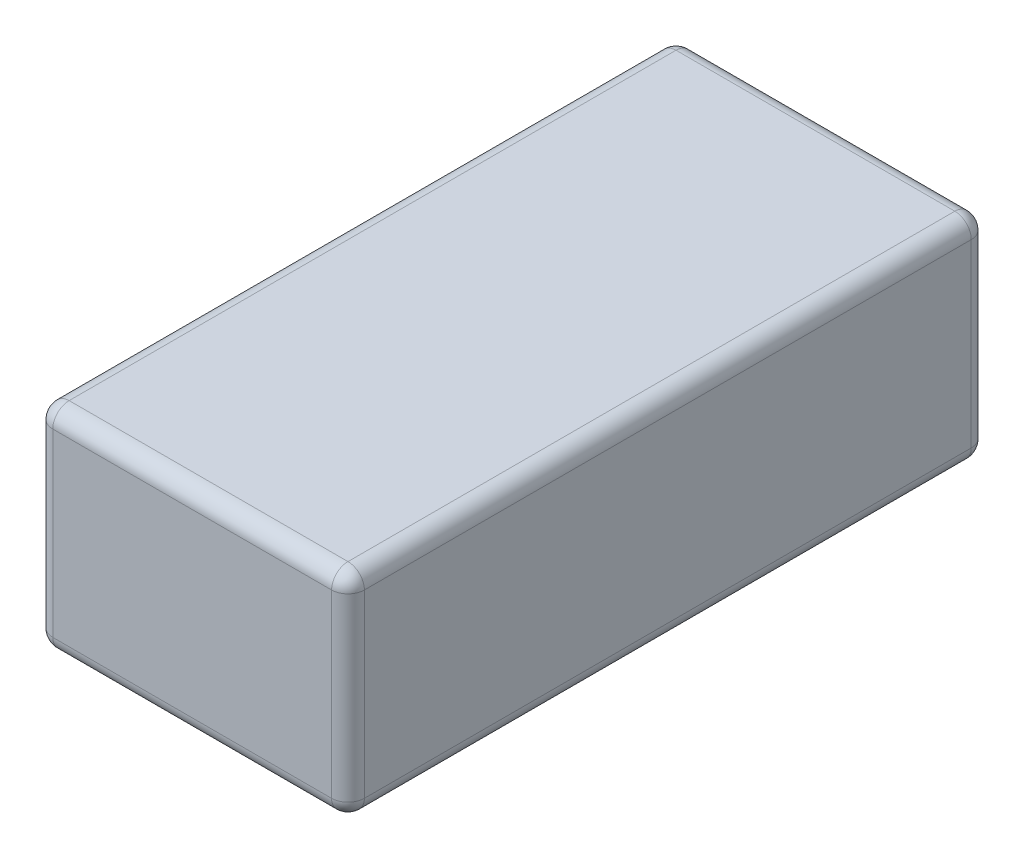
SolidWorks part; units mm, degrees
ref_plane "Front Plane" through (0, 0, 0) normal (0, 0, 1) x (1, 0, 0)
ref_plane "Top Plane" through (0, 0, 0) normal (0, 1, 0) x (1, 0, 0)
ref_plane "Right Plane" through (0, 0, 0) normal (1, 0, 0) x (0, 0, -1)
sketch "Sketch1" plane through (0, 0, 0) normal (0, 0, 1) x (1, 0, 0)
  line L1 (47.5, -32.5) -> (-47.5, -32.5)
  line L2 (47.5, -32.5) -> (47.5, 32.5)
  line L3 (47.5, 32.5) -> (-47.5, 32.5)
  line L4 (-47.5, -32.5) -> (-47.5, 32.5)
  line L5 (47.5, -32.5) -> (-47.5, 32.5) construction
  line L6 (47.5, 32.5) -> (-47.5, -32.5) construction
  point P0 (0, 0)
  dimension "D1" = 95
  dimension "D2" = 65
extrude "Boss-Extrude1" add sketch "Sketch1" against normal blind 195
fillet "Fillet1" radius 5 12 edges at (0, -32.5, -195) (-47.5, -32.5, -97.5) (-47.5, 0, -195) (0, -32.5, 0) (-47.5, 0, 0) (47.5, 0, -195) (47.5, -32.5, -97.5) (47.5, 0, 0) (-47.5, 32.5, -97.5) (0, 32.5, -195) (47.5, 32.5, -97.5) (0, 32.5, 0)
